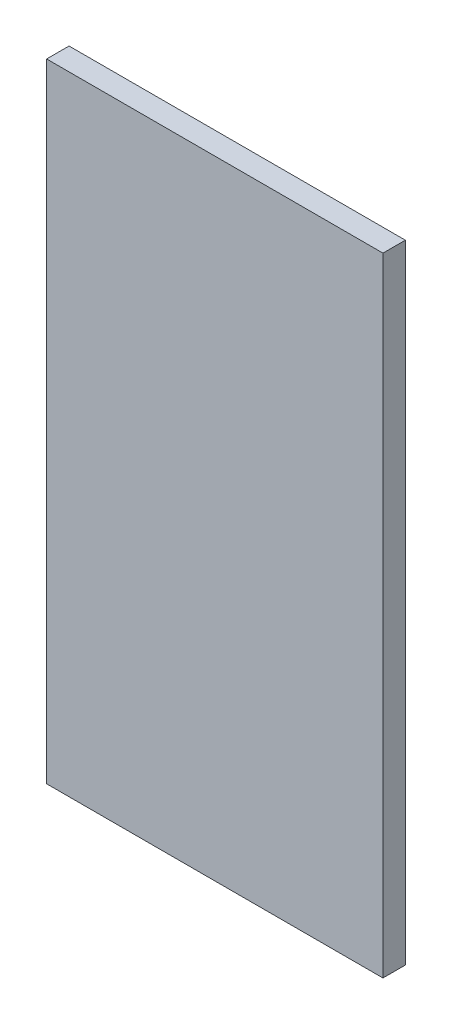
SolidWorks part; units mm, degrees
ref_plane "Front Plane" through (0, 0, 0) normal (0, 0, 1) x (1, 0, 0)
ref_plane "Top Plane" through (0, 0, 0) normal (0, 1, 0) x (1, 0, 0)
ref_plane "Right Plane" through (0, 0, 0) normal (1, 0, 0) x (0, 0, -1)
sketch "Sketch1" plane through (0, 0, 0) normal (0, 0, 1) x (1, 0, 0)
  line L1 (0, 0) -> (95.25, 0)
  line L2 (0, 0) -> (0, 177.8)
  line L3 (0, 177.8) -> (95.25, 177.8)
  line L4 (95.25, 0) -> (95.25, 177.8)
  dimension "D1" = 177.8
  dimension "D2" = 95.25
extrude "Boss-Extrude1" add sketch "Sketch1" along normal blind 6.35
